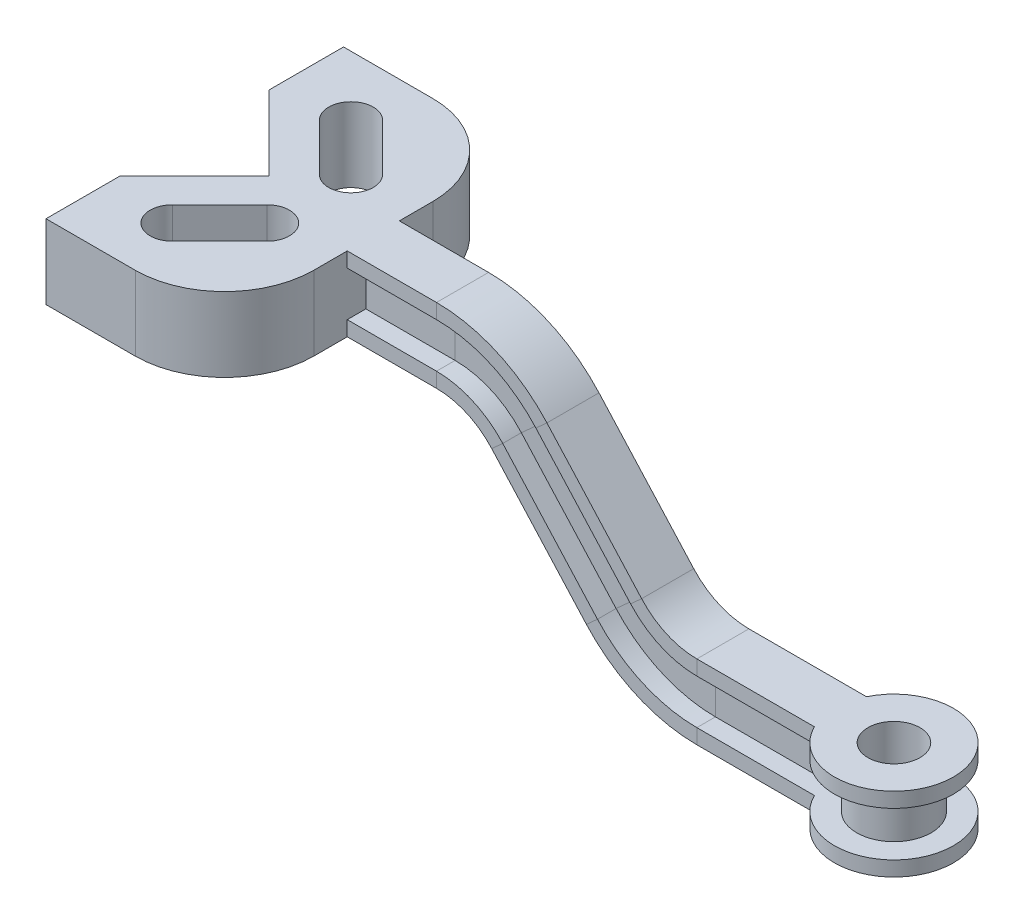
SolidWorks part; units mm, degrees
ref_plane "前基準面" through (0, 0, 0) normal (0, 0, 1) x (1, 0, 0)
ref_plane "上基準面" through (0, 0, 0) normal (0, 1, 0) x (1, 0, 0)
ref_plane "右基準面" through (0, 0, 0) normal (1, 0, 0) x (0, 0, -1)
sketch "草圖1" plane through (0, 0, 0) normal (0, 1, 0) x (1, 0, 0)
  line L0 (-120, 100) -> (-60, 100)
  line L1 (0, 40) -> (0, -40)
  line L2 (-60, -100) -> (-120, -100)
  line L6 (-120, 100) -> (-120, 50)
  line L7 (-120, 50) -> (-70, 0)
  line L8 (-70, 0) -> (-120, -50)
  line L9 (-120, -50) -> (-120, -100)
  line L10 (-75, 60) -> (-43.1802, 28.1802) construction
  line L11 (-64.3934, 70.6066) -> (-32.5736, 38.7868)
  line L12 (-85.6066, 49.3934) -> (-53.7868, 17.5736)
  line L13 (-85.6066, 0) -> (19.2558, 0) construction
  line L14 (-75, -60) -> (-43.1802, -28.1802) construction
  line L15 (-64.3934, -70.6066) -> (-32.5736, -38.7868)
  line L16 (-85.6066, -49.3934) -> (-53.7868, -17.5736)
  arc A0 (-64.3934, 70.6066) -> (-85.6066, 49.3934) centre (-75, 60) ccw
  arc A1 (-53.7868, 17.5736) -> (-32.5736, 38.7868) centre (-43.1802, 28.1802) ccw
  arc A2 (-64.3934, -70.6066) -> (-85.6066, -49.3934) centre (-75, -60) cw
  arc A3 (-53.7868, -17.5736) -> (-32.5736, -38.7868) centre (-43.1802, -28.1802) cw
  arc A4 (-60, 100) -> (0, 40) centre (-60, 40) cw
  arc A5 (-60, -100) -> (0, -40) centre (-60, -40) ccw
  point P4 (-59.0901, 44.0901)
  point P18 (-59.0901, -44.0901)
  point P26 (0, 100)
  point P29 (0, -100)
  dimension "D1" = 15
  dimension "D8" = 60
  dimension "D9" = 60
  dimension "D2" = 200
  dimension "D3" = 120
  dimension "D4" = 45
  dimension "D5" = 40
  dimension "D6" = 45
  dimension "D7" = 50
extrude "填料-伸長1" add sketch "草圖1" along normal blind 50
sketch "草圖2" plane through (0, 0, 0) normal (0, 0, 1) x (1, 0, 0)
  line L0 (0, 50) -> (60, 50)
  line L1 (0, 50) -> (0, 0) construction
  line L2 (134.2268, 17.0103) -> (197.8866, -53.5052)
  line L3 (235, -70) -> (350, -70)
  arc A0 (134.2268, 17.0103) -> (60, 50) centre (60, -50) ccw
  arc A1 (235, -70) -> (197.8866, -53.5052) centre (235, -20) cw
  dimension "D1" = 100
  dimension "D2" = 50
  dimension "D3" = 235
  dimension "D4" = 60
  dimension "D5" = 70
  dimension "D6" = 350
sketch "草圖3" plane through (0, 0, 0) normal (1, 0, 0) x (0, 0, -1)
  line L0 (17.5, 50) -> (-17.5, 50)
  line L1 (-17.5, 50) -> (-17.5, 40)
  line L2 (-17.5, 40) -> (-5, 40)
  line L3 (-5, 40) -> (-5, 10)
  line L4 (-5, 10) -> (-17.5, 10)
  line L5 (-17.5, 10) -> (-17.5, 0)
  line L6 (-17.5, 0) -> (17.5, 0)
  line L7 (0, 50) -> (0, 17.0103) construction
  line L8 (0, 55.4023) -> (0, -26.8051) construction
  line L9 (0, 17.0103) -> (0, -53.5052) construction
  line L10 (17.5, 10) -> (17.5, 0)
  line L11 (5, 10) -> (17.5, 10)
  line L12 (5, 40) -> (5, 10)
  line L13 (17.5, 40) -> (5, 40)
  line L14 (17.5, 50) -> (17.5, 40)
  point P15 (0, 0)
  point P20 (0, 50)
  dimension "D1" = 10
  dimension "D2" = 10
  dimension "D3" = 10
  dimension "D4" = 50
  dimension "D5" = 35
sweep "掃出1" add profiles "草圖3" path "草圖2"
sketch "草圖4" plane through (0, 0, 0) normal (0, 0, 1) x (1, 0, 0)
  line L0 (350, -70) -> (390, -70)
  line L1 (350, -70) -> (350, -120)
  line L2 (350, -47.2378) -> (350, -129.7645) construction
  line L3 (390, -70) -> (390, -80)
  line L4 (390, -80) -> (375, -80)
  line L5 (350, 40) -> (350, 10) construction
  line L6 (375, -80) -> (375, -110)
  line L7 (235, -70) -> (350, -70) construction
  line L8 (375, -110) -> (390, -110)
  line L9 (390, -110) -> (390, -120)
  line L10 (390, -120) -> (350, -120)
  dimension "D1" = 80
  dimension "D2" = 50
  dimension "D3" = 50
  dimension "D4" = 10
  dimension "D5" = 10
revolve "旋轉1" add sketch "草圖4" angle 360 about L2
sketch "草圖5" plane through (0, -70, 0) normal (0, 1, 0) x (1, 0, 0)
  line L0 (235, 0) -> (350, 0) construction
  circle A0 centre (350, 0) radius 17.5
  dimension "D1" = 35
extrude "除料-伸長1" cut sketch "草圖5" against normal through all
